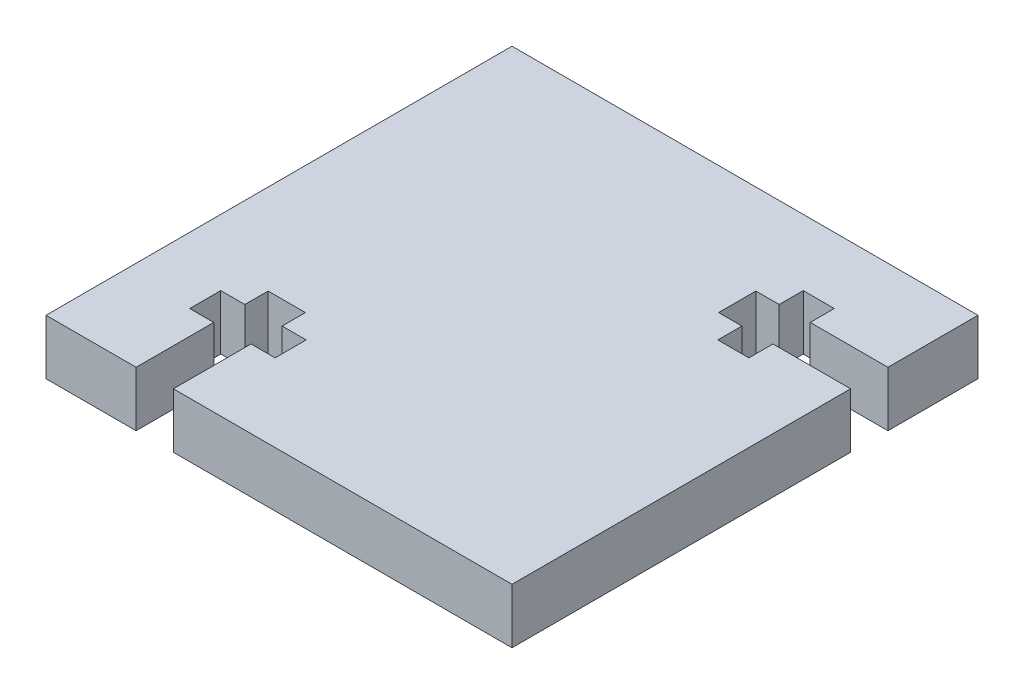
SolidWorks part; units mm, degrees
ref_plane "Front Plane" through (0, 0, 0) normal (0, 0, 1) x (1, 0, 0)
ref_plane "Top Plane" through (0, 0, 0) normal (0, 1, 0) x (1, 0, 0)
ref_plane "Right Plane" through (0, 0, 0) normal (1, 0, 0) x (0, 0, -1)
sketch "Sketch1" plane through (0, 0, 0) normal (0, 1, 0) x (1, 0, 0)
  line L0 (-30.734, 0) -> (-30.734, 6.35)
  line L1 (-38.1, 38.1) -> (0, 38.1)
  line L2 (-38.1, 38.1) -> (-38.1, 0)
  line L3 (-38.1, 0) -> (-30.734, 0)
  line L4 (0, 38.1) -> (0, 30.734)
  line L5 (-30.734, 6.35) -> (-32.7025, 6.35)
  line L6 (-32.7025, 6.35) -> (-32.7025, 8.89)
  line L7 (-32.7025, 8.89) -> (-30.734, 8.89)
  line L8 (-25.7175, 8.89) -> (-25.7175, 6.35)
  line L9 (-25.7175, 6.35) -> (-27.686, 6.35)
  line L10 (-27.686, 6.35) -> (-27.686, 0)
  line L11 (-29.21, 8.89) -> (-29.21, 0) construction
  line L12 (-30.734, 6.35) -> (-27.686, 6.35) construction
  line L13 (-29.21, 8.89) -> (-29.21, 29.21) construction
  line L14 (-29.21, 29.21) -> (0, 29.21) construction
  line L15 (-38.1, 29.21) -> (-29.21, 29.21) construction
  line L16 (-29.21, 29.21) -> (-29.21, 38.1) construction
  line L17 (-8.89, 25.7175) -> (-8.89, 27.686)
  line L18 (-8.89, 32.7025) -> (-6.35, 32.7025)
  line L19 (-6.35, 25.7175) -> (-8.89, 25.7175)
  line L20 (-6.35, 27.686) -> (-6.35, 25.7175)
  line L21 (0, 27.686) -> (-6.35, 27.686)
  line L22 (-6.35, 30.734) -> (0, 30.734)
  line L23 (-6.35, 32.7025) -> (-6.35, 30.734)
  line L24 (0, 30.734) -> (0, 27.686) construction
  line L25 (-25.7175, 8.89) -> (-29.21, 29.21) construction
  line L26 (-27.686, 0) -> (0, 0)
  line L27 (0, 27.686) -> (0, 0)
  line L28 (-29.21, 29.21) -> (-8.89, 25.7175) construction
  line L29 (-6.35, 30.734) -> (-6.35, 27.686) construction
  line L30 (-30.734, 8.89) -> (-30.734, 10.795)
  line L31 (-30.734, 10.795) -> (-27.686, 10.795)
  line L32 (-27.686, 10.795) -> (-27.686, 8.89)
  line L33 (-27.686, 8.89) -> (-25.7175, 8.89)
  line L34 (-8.89, 27.686) -> (-10.795, 27.686)
  line L35 (-10.795, 27.686) -> (-10.795, 30.734)
  line L36 (-10.795, 30.734) -> (-8.89, 30.734)
  line L37 (-8.89, 30.734) -> (-8.89, 32.7025)
  point P17 (-29.21, 6.35)
  point P27 (0, 29.21)
  point P31 (-28.9696, 28.9696)
  dimension "D1" = 38.1
  dimension "D2" = 38.1
  dimension "D3" = 3.048
  dimension "D4" = 8.89
  dimension "D5" = 2.54
  dimension "D6" = 8.89
  dimension "D7" = 6.985
  dimension "D8" = 1.905
extrude "Boss-Extrude1" add sketch "Sketch1" along normal blind 4.4958
